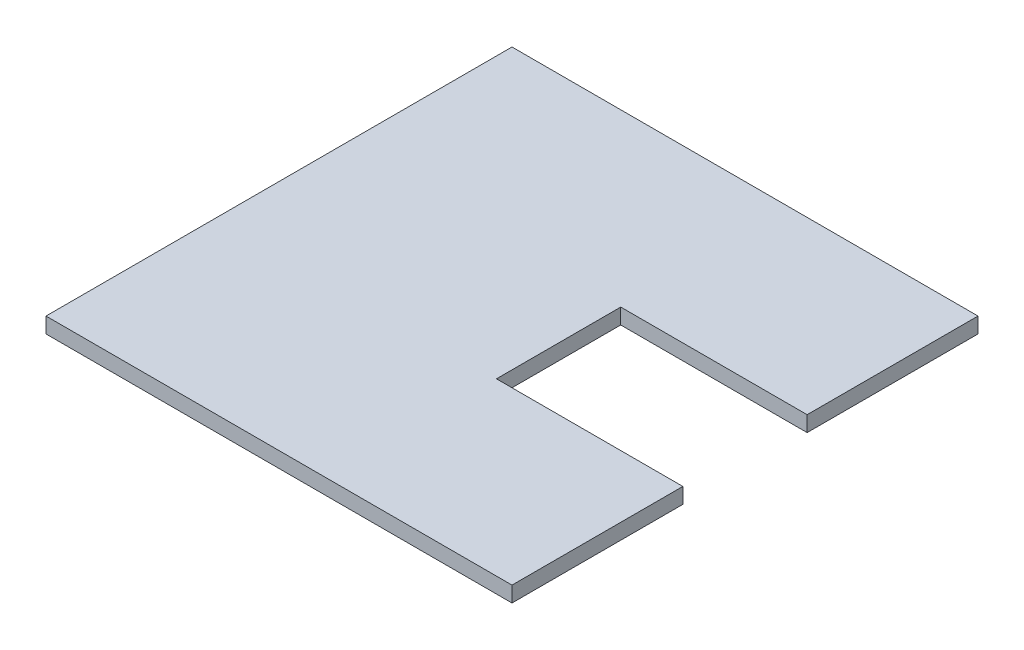
SolidWorks part; units mm, degrees
material "Beech"
ref_plane "Front Plane" through (0, 0, 0) normal (0, 0, 1) x (1, 0, 0)
ref_plane "Top Plane" through (0, 0, 0) normal (0, 1, 0) x (1, 0, 0)
ref_plane "Right Plane" through (0, 0, 0) normal (1, 0, 0) x (0, 0, -1)
sketch "Sketch1" plane through (0, 0, 0) normal (0, 1, 0) x (1, 0, 0)
  line L0 (134.1892, 110.7573) -> (134.1892, 165.7573)
  line L1 (-15.8108, 15.7573) -> (134.1892, 15.7573)
  line L2 (-15.8108, 15.7573) -> (-15.8108, 165.7573)
  line L3 (-15.8108, 165.7573) -> (134.1892, 165.7573)
  line L4 (134.1892, 15.7573) -> (134.1892, 70.7573)
  line L6 (134.1892, 70.7573) -> (74.1892, 70.7573)
  line L7 (134.1892, 110.7573) -> (74.1892, 110.7573)
  line L8 (74.1892, 70.7573) -> (74.1892, 90.7573)
  line L9 (74.1892, 90.7573) -> (74.1892, 110.7573)
  line L10 (74.1892, 110.7573) -> (73.4683, 111.6338)
extrude "Boss-Extrude1" add sketch "Sketch1" along normal blind 5
